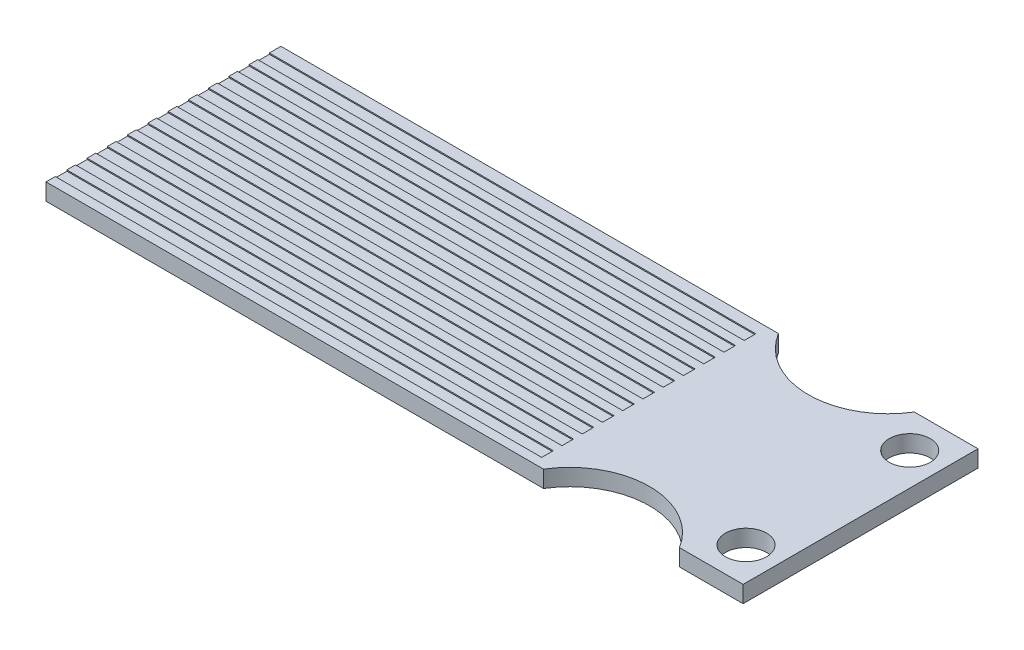
SolidWorks part; units mm, degrees
ref_plane "Front Plane" through (0, 0, 0) normal (0, 0, 1) x (1, 0, 0)
ref_plane "Top Plane" through (0, 0, 0) normal (0, 1, 0) x (1, 0, 0)
ref_plane "Right Plane" through (0, 0, 0) normal (1, 0, 0) x (0, 0, -1)
sketch "Sketch1" plane through (0, 0, 0) normal (0, 1, 0) x (1, 0, 0)
  line L0 (30.125, 10.15) -> (24.625, 10.15)
  line L1 (-30.125, 10.15) -> (12.875, 10.15)
  line L2 (-30.125, 10.15) -> (-30.125, -10.15)
  line L3 (-30.125, -10.15) -> (12.875, -10.15)
  line L4 (30.125, 10.15) -> (30.125, -10.15)
  line L5 (24.625, 10.15) -> (30.125, 10.15)
  line L6 (24.625, -10.15) -> (30.125, -10.15)
  line L7 (-30.125, 10.15) -> (12.875, 10.15)
  arc A0 (12.875, 10.15) -> (24.625, 10.15) centre (18.75, 13.7558) ccw
  arc A1 (12.875, -10.15) -> (24.625, -10.15) centre (18.75, -13.7558) cw
  point P0 (0, 0)
  point P13 (12.875, 10.15)
  dimension "D1" = 20.3
  dimension "D2" = 60.25
  dimension "D3" = 5.5
  dimension "D4" = 43
extrude "Boss-Extrude1" add sketch "Sketch1" along normal blind 1.45 contours L3 A1 L6 L4 L0 A0 L1 L2
sketch "Sketch2" plane through (0, 1.45, 0) normal (0, 1, 0) x (1, 0, 0)
  circle A0 centre (27.3, 7.075) radius 1.775
  circle A1 centre (27.3, -7.075) radius 1.775
  dimension "D1" = 3.55
extrude "Cut-Extrude1" cut sketch "Sketch2" against normal through all
sketch "Sketch3" plane through (0, 1.45, 0) normal (0, 1, 0) x (1, 0, 0)
  line L0 (-30.125, -10.15) -> (12.875, -10.15) construction
  line L1 (-30.125, 10.15) -> (11.9193, 10.15)
  line L2 (-30.125, 10.15) -> (-30.125, -10.15)
  line L3 (-30.125, -10.15) -> (11.9193, -10.15)
  line L4 (11.9193, 10.15) -> (11.9193, -10.15)
  line L5 (-30.125, 9.15) -> (11.9193, 9.15)
  line L6 (-20.125, 9.15) -> (-20.125, 8.15)
  line L7 (-30.125, 9.15) -> (11.9193, 9.15)
  line L8 (-30.125, 9.15) -> (-30.125, 8.15)
  line L9 (-30.125, 8.15) -> (11.9193, 8.15)
  line L10 (11.9193, 9.15) -> (11.9193, 8.15)
  line L11 (-20.125, 9.15) -> (11.9193, 9.15)
  line L13 (-20.125, 8.15) -> (11.9193, 8.15)
  line L14 (-20.125, 7.4) -> (-20.125, 6.4)
  line L15 (-20.125, 7.4) -> (11.9193, 7.4)
  line L17 (-20.125, 6.4) -> (11.9193, 6.4)
  line L18 (-20.125, 5.65) -> (-20.125, 4.65)
  line L19 (-20.125, 5.65) -> (11.9193, 5.65)
  line L21 (-20.125, 4.65) -> (11.9193, 4.65)
  line L22 (-20.125, 3.9) -> (-20.125, 2.9)
  line L23 (-20.125, 3.9) -> (11.9193, 3.9)
  line L25 (-20.125, 2.9) -> (11.9193, 2.9)
  line L26 (-20.125, 2.15) -> (-20.125, 1.15)
  line L27 (-20.125, 2.15) -> (11.9193, 2.15)
  line L29 (-20.125, 1.15) -> (11.9193, 1.15)
  line L30 (-20.125, 0.4) -> (-20.125, -0.6)
  line L31 (-20.125, 0.4) -> (11.9193, 0.4)
  line L33 (-20.125, -0.6) -> (11.9193, -0.6)
  line L34 (-20.125, -1.35) -> (-20.125, -2.35)
  line L35 (-20.125, -1.35) -> (11.9193, -1.35)
  line L37 (-20.125, -2.35) -> (11.9193, -2.35)
  line L38 (-20.125, -3.1) -> (-20.125, -4.1)
  line L39 (-20.125, -3.1) -> (11.9193, -3.1)
  line L41 (-20.125, -4.1) -> (11.9193, -4.1)
  line L42 (-20.125, -4.85) -> (-20.125, -5.85)
  line L43 (-20.125, -4.85) -> (11.9193, -4.85)
  line L45 (-20.125, -5.85) -> (11.9193, -5.85)
  line L46 (-20.125, -6.6) -> (-20.125, -7.6)
  line L47 (-20.125, -6.6) -> (11.9193, -6.6)
  line L49 (-20.125, -7.6) -> (11.9193, -7.6)
  line L50 (-20.125, -8.35) -> (-20.125, -9.35)
  line L51 (-20.125, -8.35) -> (11.9193, -8.35)
  line L53 (-20.125, -9.35) -> (11.9193, -9.35)
  line L54 (-30.125, 7.4) -> (-30.125, 6.4)
  line L55 (-30.125, 7.4) -> (11.9193, 7.4)
  line L56 (11.9193, 7.4) -> (11.9193, 6.4)
  line L57 (-30.125, 6.4) -> (11.9193, 6.4)
  line L58 (-30.125, 5.65) -> (-30.125, 4.65)
  line L59 (-30.125, 5.65) -> (11.9193, 5.65)
  line L60 (11.9193, 5.65) -> (11.9193, 4.65)
  line L61 (-30.125, 4.65) -> (11.9193, 4.65)
  line L62 (-30.125, 3.9) -> (-30.125, 2.9)
  line L63 (-30.125, 3.9) -> (11.9193, 3.9)
  line L64 (11.9193, 3.9) -> (11.9193, 2.9)
  line L65 (-30.125, 2.9) -> (11.9193, 2.9)
  line L66 (-30.125, 2.15) -> (-30.125, 1.15)
  line L67 (-30.125, 2.15) -> (11.9193, 2.15)
  line L68 (11.9193, 2.15) -> (11.9193, 1.15)
  line L69 (-30.125, 1.15) -> (11.9193, 1.15)
  line L70 (-30.125, 0.4) -> (-30.125, -0.6)
  line L71 (-30.125, 0.4) -> (11.9193, 0.4)
  line L72 (11.9193, 0.4) -> (11.9193, -0.6)
  line L73 (-30.125, -0.6) -> (11.9193, -0.6)
  line L74 (-30.125, -1.35) -> (-30.125, -2.35)
  line L75 (-30.125, -1.35) -> (11.9193, -1.35)
  line L76 (11.9193, -1.35) -> (11.9193, -2.35)
  line L77 (-30.125, -2.35) -> (11.9193, -2.35)
  line L78 (-30.125, -3.1) -> (-30.125, -4.1)
  line L79 (-30.125, -3.1) -> (11.9193, -3.1)
  line L80 (11.9193, -3.1) -> (11.9193, -4.1)
  line L81 (-30.125, -4.1) -> (11.9193, -4.1)
  line L82 (-30.125, -4.85) -> (-30.125, -5.85)
  line L83 (-30.125, -4.85) -> (11.9193, -4.85)
  line L84 (11.9193, -4.85) -> (11.9193, -5.85)
  line L85 (-30.125, -5.85) -> (11.9193, -5.85)
  line L86 (-30.125, -6.6) -> (-30.125, -7.6)
  line L87 (-30.125, -6.6) -> (11.9193, -6.6)
  line L88 (11.9193, -6.6) -> (11.9193, -7.6)
  line L89 (-30.125, -7.6) -> (11.9193, -7.6)
  line L90 (-30.125, -8.35) -> (-30.125, -9.35)
  line L91 (-30.125, -8.35) -> (11.9193, -8.35)
  line L92 (11.9193, -8.35) -> (11.9193, -9.35)
  line L93 (-30.125, -9.35) -> (11.9193, -9.35)
  line L94 (21.9193, -8.35) -> (21.9193, -9.35) [skipped]
  line L95 (21.9193, 9.15) -> (21.9193, 8.15) [skipped]
  line L96 (21.9193, 7.4) -> (21.9193, 6.4) [skipped]
  line L97 (21.9193, 5.65) -> (21.9193, 4.65) [skipped]
  line L98 (21.9193, 3.9) -> (21.9193, 2.9) [skipped]
  line L99 (21.9193, 2.15) -> (21.9193, 1.15) [skipped]
  line L100 (21.9193, 0.4) -> (21.9193, -0.6) [skipped]
  line L101 (21.9193, -1.35) -> (21.9193, -2.35) [skipped]
  line L102 (21.9193, -4.85) -> (21.9193, -5.85) [skipped]
  line L103 (21.9193, -6.6) -> (21.9193, -6.8183) [skipped]
  line L104 (21.9193, -6.6) -> (21.9193, -6.8183) [skipped]
  dimension "D1" = 1
  dimension "D2" = 1
  dimension "D3" = 2
  dimension "D4" = 11
extrude "Cut-Extrude2" cut sketch "Sketch3" against normal blind 0.1 contours L2 L9 L4 L5 | L54 L57 L56 L55 | L58 L61 L60 L59 | L62 L65 L64 L63 | L66 L69 L68 L67 | L70 L73 L72 L71 | L74 L77 L76 L75 | L78 L81 L80 L79 | L82 L85 L84 L83 | L86 L89 L88 L87 | L90 L93 L92 L91
